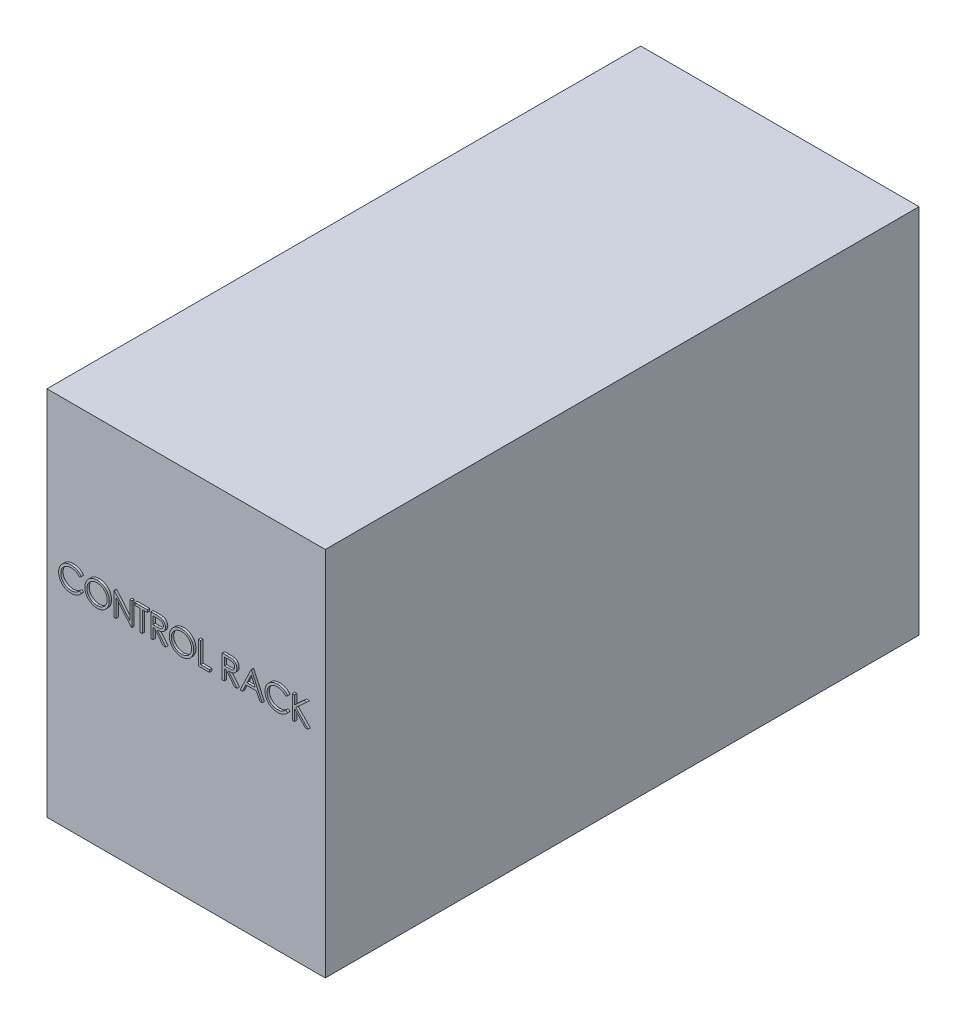
SolidWorks part; units mm, degrees
ref_plane "Front Plane" through (0, 0, 0) normal (0, 0, 1) x (1, 0, 0)
ref_plane "Top Plane" through (0, 0, 0) normal (0, 1, 0) x (1, 0, 0)
ref_plane "Right Plane" through (0, 0, 0) normal (1, 0, 0) x (0, 0, -1)
sketch "Sketch1" plane through (0, 0, 0) normal (0, 0, 1) x (1, 0, 0)
  line L1 (0, 0) -> (-600, 0)
  line L2 (0, 0) -> (0, 800)
  line L3 (0, 800) -> (-600, 800)
  line L4 (-600, 0) -> (-600, 800)
  dimension "D1" = 600
  dimension "D2" = 800
extrude "Boss-Extrude1" add sketch "Sketch1" along normal blind 1280
sketch "Sketch2" plane through (0, 0, 1280) normal (0, 0, 1) x (1, 0, 0)
  text T0 "CONTROL RACK" font "Century Gothic" height 50
  point P1 (0, 0)
extrude "Boss-Extrude2" add sketch "Sketch2" along normal blind 5
